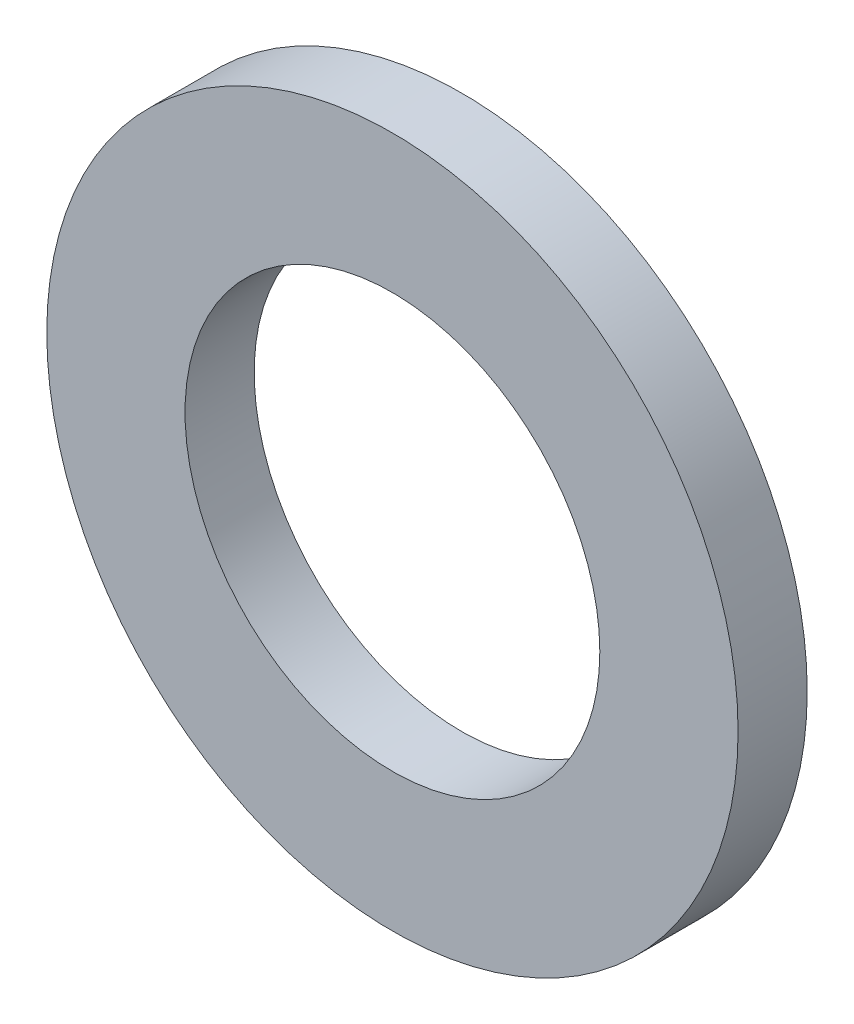
SolidWorks part; units mm, degrees
material "Aluminum Bronze"
ref_plane "Front Plane" through (0, 0, 0) normal (0, 0, 1) x (1, 0, 0)
ref_plane "Top Plane" through (0, 0, 0) normal (0, 1, 0) x (1, 0, 0)
ref_plane "Right Plane" through (0, 0, 0) normal (1, 0, 0) x (0, 0, -1)
sketch "Sketch1" plane through (0, 0, 0) normal (0, 0, 1) x (1, 0, 0)
  circle A0 centre (0, 0) radius 4.7625
  circle A1 centre (0, 0) radius 7.9375
  dimension "D1" = 9.525
  dimension "D2" = 15.875
extrude "Boss-Extrude1" add sketch "Sketch1" along normal blind 1.5875
